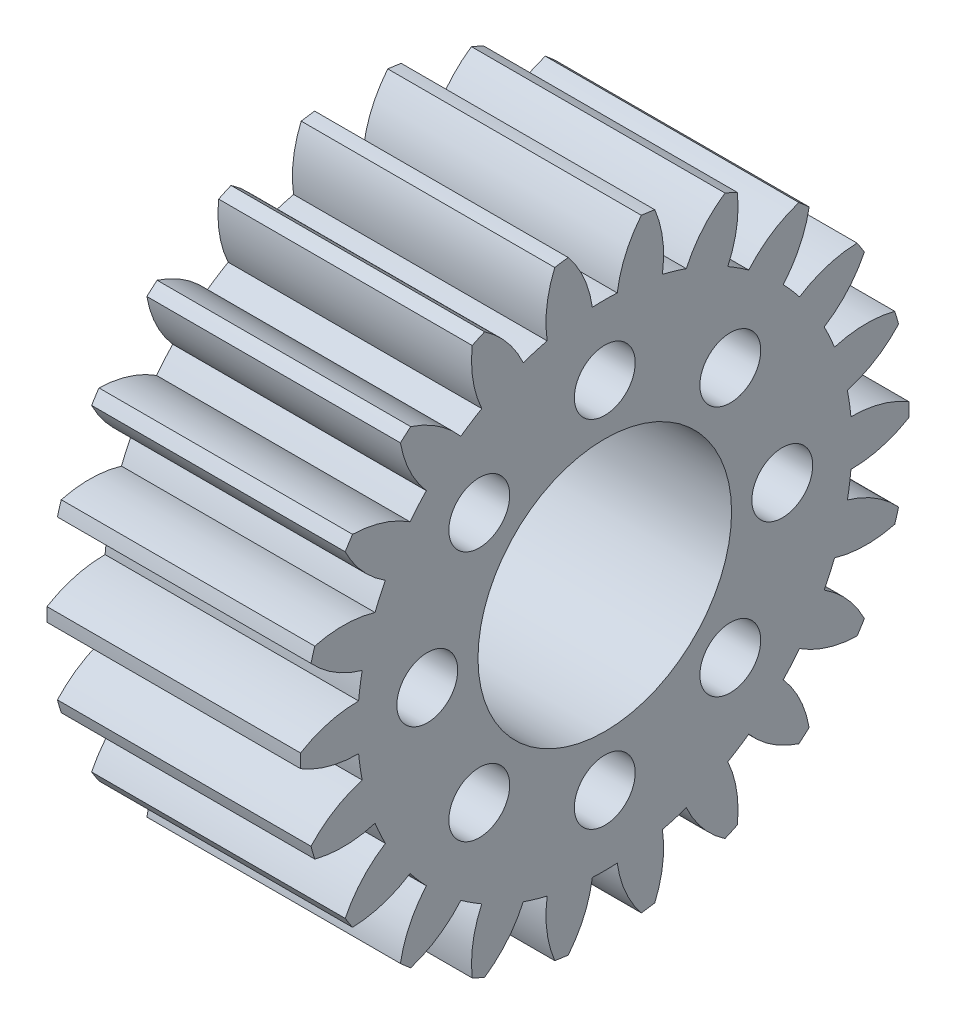
SolidWorks part; units mm, degrees
ref_plane "Plane1" through (0, 0, 0) normal (0, 0, 1) x (1, 0, 0)
ref_plane "Plane2" through (0, 0, 0) normal (0, 1, 0) x (1, 0, 0)
ref_plane "Plane3" through (0, 0, 0) normal (1, 0, 0) x (0, 0, -1)
sketch "HoldingSke" plane through (0, 0, 0) normal (0, 1, 0) x (1, 0, 0)
  line L0 (0, 0) -> (0.9272, -0.3746)
  line L1 (-15, 0) -> (100, 0) construction
  line L2 (0, 0) -> (-2.1039, 2.3779)
  line L3 (0, 0) -> (-11.863, 4.5341)
  line L4 (0, 0) -> (8.0072, 3.2351)
  line L5 (0, 0) -> (-46.8476, -17.4728)
  line L6 (0, 0) -> (-8.2896, -5.593)
  line L7 (-2.1039, 2.3779) -> (8.6586, 51.2059)
  line L8 (-76.2, 54.61) -> (-74.4, 54.61)
  line L9 (-71.009, 38.7566) -> (-53.1078, 45.2721)
  line L10 (-76.2, 71.12) -> (104.1128, 71.12)
  line L11 (0, 0) -> (-10, 0)
  line L12 (-76.2, 101.6) -> (-76.162, 101.6)
  line L13 (24.9733, 27.94) -> (52.9518, 28.4284)
  line L14 (24.9733, 27.94) -> (24.9743, 27.94)
  line L15 (24.9733, 27.94) -> (100.4006, 29.5858)
  line L16 (-63.627, -1) -> (-12.827, -1)
  circle A0 centre (0, 0) radius 5
  circle A1 centre (0, 0) radius 9.749
  circle A2 centre (0, 0) radius 37.5
  circle A3 centre (0, 0) radius 5
  dimension "MHD" = 19.498
  dimension "Hub_dia" = 75
  dimension "Bore" = 10
  dimension "MBD" = 10
  dimension "Num_teeth" = 22
  dimension "Pitch" = 1
  dimension "Overall_len" = 50
  dimension "Show_teeth" = 22
  dimension "Thickness" = 10
  dimension "OAL" = 50.0001
  dimension "T_dim" = 1.8
  dimension "Ap" = 20
  dimension "H" = 19.05
  dimension "Pitch_radius" = 180.3128
  dimension "Width" = 10
  dimension "Backlash" = 0.038
  dimension "Addendum_fac" = 1
  dimension "Dedendum_fac" = 1.25
  dimension "Clearance_fac" = 0.25
  dimension "Dedendum_add" = 0.001
  dimension "Module" = 1
sketch "BasProSke" plane through (0, 0, 0) normal (0, 1, 0) x (1, 0, 0)
  line L0 (-10, 0) -> (60, 0) construction
  line L1 (0, 0) -> (0, 12)
  line L2 (0, 0) -> (10, 0)
  line L3 (10, 0) -> (10, 12)
  line L4 (10, 12) -> (0, 12)
  dimension "Thickness" = 10
  dimension "Diameter" = 24
revolve "Base-Revolve" add sketch "BasProSke" angle 360 about L0
sketch "TooCutSke" plane through (0, 0, 0) normal (1, 0, 0) x (0, 0, -1)
  line L1 (0, 0) -> (0, 107) construction
  line L2 (0, 0) -> (-0.8512, 10.967) construction
  line L3 (0, 0) -> (-3.1242, 21.7296) construction
  line L4 (-0.8512, 10.967) -> (-1.5621, 10.8648) construction
  arc A0 (0.491, 9.7366) -> (-0.491, 9.7366) centre (0, 0) ccw
  arc A1 (1.4609, 11.9363) -> (-1.4609, 11.9363) centre (0, 0) ccw
  circle A2 centre (0, 0) radius 11 construction
  circle A3 centre (0, 0) radius 10.3366 construction
  arc A4 (-0.491, 9.7366) -> (-1.4609, 11.9363) centre (-4.8488, 9.1288) ccw
  arc A5 (1.4609, 11.9363) -> (0.491, 9.7366) centre (4.8488, 9.1288) ccw
  dimension "Root_dia" = 19.498
  dimension "Overcut_dia" = 24.0508
  dimension "Pitch_dia" = 22
  dimension "Base_dia" = 20.6732
  dimension "Flank_rad" = 4.4
  dimension "Half_ang" = 8.182
  dimension "Half_CT" = 0.7182
extrude "ToothCut" cut sketch "TooCutSke" along normal through all
fillet "Breaks" [suppressed] radius 0.02
fillet "RootFillets" [suppressed] radius 0.251
pattern_circular "TeethCuts" count 22 every 16.364 about axis through (-10, 0, 0) along (1, 0, 0) of "ToothCut", "RootFillets", "Breaks"
sketch "HubNeaOneSke" plane through (0, 0, 0) normal (-1, 0, 0) x (0, 0, 1)
  circle A0 centre (0, 0) radius 9.749
  dimension "Diameter" = 19.498
extrude "HubNearOne" [suppressed] add sketch "HubNeaOneSke" along normal blind 40.0001
sketch "HubNeaBotSke" plane through (0, 0, 0) normal (-1, 0, 0) x (0, 0, 1)
  circle A0 centre (0, 0) radius 9.749
  dimension "Diameter" = 19.498
extrude "HubNearBoth" [suppressed] add sketch "HubNeaBotSke" along normal blind 20
ref_plane "FarPln" through (10, 0, 0) normal (1, 0, 0) x (0, 0, -1)
sketch "HubFarSke" plane through (10, 0, 0) normal (1, 0, 0) x (0, 0, -1)
  circle A0 centre (0, 0) radius 9.749
  dimension "Diameter" = 19.498
extrude "HubFar" [suppressed] add sketch "HubFarSke" along normal blind 20
sketch "BorSke" plane through (0, 0, 0) normal (1, 0, 0) x (0, 0, -1)
  circle A0 centre (0, 0) radius 5
  dimension "Diameter" = 10
extrude "Bore" cut sketch "BorSke" along normal mid plane 100.0001
sketch "KeySke" plane through (0, 0, 0) normal (1, 0, 0) x (0, 0, -1)
  line L0 (-2, 0) -> (-2, 6.8)
  line L1 (-2, 6.8) -> (2, 6.8)
  line L2 (2, 6.8) -> (2, 0)
  line L3 (0, 0) -> (0, 34) construction
  line L4 (-2, 0) -> (2, 0)
  dimension "Offset" = 6.8
  dimension "Width" = 4
extrude "Keyway" [suppressed] cut sketch "KeySke" along normal mid plane 100.0001
pattern_circular "Keyway2" [suppressed] count 2 every 90 about axis through (-10, 0, 0) along (1, 0, 0)
hole_wizard "Dégagement M21" positions "Esquisse1" profile "Esquisse2" hole size "M2" standard "ISO" end condition up to next
sketch "Esquisse1" plane through (10, 0, 0) normal (1, 0, 0) x (0, 0, -1)
  point P0 (0, 7)
  point P8 (4.9497, 4.9497)
  point P9 (7, 0)
  point P10 (4.9497, -4.9497)
  point P11 (0, -7)
  point P12 (-4.9497, -4.9497)
  point P13 (-7, 0)
  point P14 (-4.9497, 4.9497)
  point P15 (0, 0)
  dimension "D1" = 8
sketch "Esquisse2" plane through (10, 7, 0) normal (0, 1, 0) x (0, 0, -1)
  line L0 (0, 0) -> (0, 10)
  line L1 (0, 10) -> (1.2, 10)
  line L2 (1.2, 10) -> (1.2, 0)
  line L5 (1.2, 0) -> (0, 0)
  line L11 (0, -6.35) -> (0, 107.95) construction
  dimension "Diamètre du perçage jusqu'au prochain" = 2.4
  dimension "Profondeur du perçage jusqu'au prochain" = 10
equation "' \"Module@HoldingSke\" = 6.35"
equation "' \"Num_teeth@HoldingSke\" = 12"
equation "' \"Ap@HoldingSke\" =  20"
equation "' \"Ap@HoldingSke\" = 20"
equation "' \"Width@HoldingSke\" = 0.5 * 25.4"
equation "' \"Hub_dia@HoldingSke\"= 1 * 25.4"
equation "' \"Hub_dia@HoldingSke\" = 1 * 25.4"
equation "' \"Overall_len@HoldingSke\" = 1.0 * 25.4"
equation "' \"Bore@HoldingSke\" = 0.75 * 25.4"
equation "' \"T_dim@HoldingSke\" = 0.1 * 25.4"
equation "' \"Width@KeySke\" = 0.25 * 25.4"
equation "' \"Show_teeth@HoldingSke\" = 13"
equation "' \"Backlash@HoldingSke\" = 0.009 * 25.4"
equation "' \"Addendum_fac@HoldingSke\" = 1.0"
equation "' \"Dedendum_fac@HoldingSke\" = 1.25"
equation "' \"Dedendum_add@HoldingSke\" = 0.00005 * 25.4"
equation "' \"Clearance_fac@HoldingSke\" = 0.25"
equation "\"Pitch@HoldingSke\" = 1 / \"Module@HoldingSke\""
equation "\"Overcut_dia@TooCutSke\" = (\"Num_teeth@HoldingSke\" + 2 * \"Addendum_fac@HoldingSke\") / \"Pitch@HoldingSke\" + 0.002 * 25.4"
equation "\"Pitch_dia@TooCutSke\" = \"Num_teeth@HoldingSke\" / \"Pitch@HoldingSke\""
equation "\"Base_dia@TooCutSke\" = \"Num_teeth@HoldingSke\" / \"Pitch@HoldingSke\" * cos((\"Ap@HoldingSke\"  * 3.14159265 / 180))"
equation "\"Root_dia@TooCutSke\" = (\"Num_teeth@HoldingSke\" + 2) / \"Pitch@HoldingSke\" - 2 * (\"Addendum_fac@HoldingSke\" + \"Dedendum_fac@HoldingSke\") / \"Pitch@HoldingSke\" - \"Dedendum_add@HoldingSke\" * 2"
equation "\"Half_ang@TooCutSke\" = 180 / \"Num_teeth@HoldingSke\""
equation "\"Half_CT@TooCutSke\" = \"Num_teeth@HoldingSke\" / \"Pitch@HoldingSke\" * sin((3.14159265 / 2 / \"Num_teeth@HoldingSke\")) / 2 - 7 * \"Backlash@HoldingSke\" / 4"
equation "\"Flank_rad@TooCutSke\" = \"Num_teeth@HoldingSke\" / \"Pitch@HoldingSke\" / 5"
equation "\"Radius@RootFillets\" = \"Clearance_fac@HoldingSke\" / \"Pitch@HoldingSke\" + \"Dedendum_add@HoldingSke\""
equation "\"Break_rad@Breaks\" = 0.02 / \"Pitch@HoldingSke\""
equation "\"Thickness@HoldingSke\" = \"Width@HoldingSke\""
equation "\"OAL@HoldingSke\" = \"Thickness@HoldingSke\""
equation "\"MHD@HoldingSke\" = (\"Num_teeth@HoldingSke\" + 2) / \"Pitch@HoldingSke\" - 2 * (\"Addendum_fac@HoldingSke\" + \"Dedendum_fac@HoldingSke\")  / \"Pitch@HoldingSke\" - \"Dedendum_add@HoldingSke\" * 2"
equation "\"MBD@HoldingSke\" = (\"Num_teeth@HoldingSke\" + 2) / \"Pitch@HoldingSke\" - 2 * (\"Addendum_fac@HoldingSke\" + \"Dedendum_fac@HoldingSke\")  / \"Pitch@HoldingSke\" - \"Dedendum_add@HoldingSke\" * 2 - 0.002 * 25.4"
equation "\"MHD@HoldingSke\" = ((sgn( \"MHD@HoldingSke\" - \"Hub_dia@HoldingSke\" )-1)*( \"MHD@HoldingSke\" - \"Hub_dia@HoldingSke\" ))/-2+ \"Hub_dia@HoldingSke\""
equation "\"MBD@HoldingSke\" = ((sgn( \"MBD@HoldingSke\" - \"Bore@HoldingSke\" )-1)*( \"MBD@HoldingSke\" - \"Bore@HoldingSke\" ))/-2+ \"Bore@HoldingSke\""
equation "\"OAL@HoldingSke\" = ((sgn( \"OAL@HoldingSke\" - \"Overall_len@HoldingSke\" )+1)*( \"OAL@HoldingSke\" - \"Overall_len@HoldingSke\" ))/2 + \"Overall_len@HoldingSke\" + 0.000002 * 25.4"
equation "\"Num_teeth@TeethCuts\" = int( \"Show_teeth@HoldingSke\" ) + 1"
equation "\"Num_teeth@TeethCuts\" = ((sgn( \"Num_teeth@TeethCuts\" - \"Num_teeth@HoldingSke\" )-1)*( \"Num_teeth@TeethCuts\" - \"Num_teeth@HoldingSke\" ))/-2+ \"Num_teeth@HoldingSke\""
equation "\"Num_teeth@TeethCuts\" = ((sgn( \"Num_teeth@TeethCuts\" - 2.0)+1)*( \"Num_teeth@TeethCuts\" - 2.0))/2 +2.0"
equation "\"Angle@TeethCuts\" = 360.0 / \"Num_teeth@HoldingSke\""
equation "\"Diameter@BasProSke\" = (\"Num_teeth@HoldingSke\" + 2 * \"Addendum_fac@HoldingSke\") / \"Pitch@HoldingSke\""
equation "\"Thickness@BasProSke\"  = \"Thickness@HoldingSke\""
equation "' \"Fillet_rad@BasProSke\" =  \"Thickness@HoldingSke\" * 0.05"
equation "' \"Fillet_rad@BasProSke\" = \"Thickness@HoldingSke\" * 0.05"
equation "\"MHD@HoldingSke\" = ((sgn( \"MHD@HoldingSke\" - \"Root_dia@TooCutSke\" )-1)*( \"MHD@HoldingSke\" - \"Root_dia@TooCutSke\" ))/-2+ \"Root_dia@TooCutSke\""
equation "\"Diameter@HubNeaOneSke\" = \"MHD@HoldingSke\""
equation "\"Length@HubNearOne\" = \"OAL@HoldingSke\" - \"Thickness@BasProSke\""
equation "\"Diameter@HubNeaBotSke\" = \"MHD@HoldingSke\""
equation "\"Length@HubNearBoth\" = ( \"OAL@HoldingSke\" - \"Thickness@BasProSke\" ) / 2.0"
equation "\"Thickness@FarPln\" = \"Thickness@BasProSke\""
equation "\"Diameter@HubFarSke\" = \"MHD@HoldingSke\""
equation "\"Length@HubFar\" = ( \"OAL@HoldingSke\" - \"Thickness@BasProSke\" ) / 2.0"
equation "\"Diameter@BorSke\" = \"MBD@HoldingSke\""
equation "\"D1@Bore\" = \"OAL@HoldingSke\" * 2.0"
equation "\"D1@Keyway\" = \"OAL@HoldingSke\" * 2.0"
equation "\"Offset@KeySke\" = \"T_dim@HoldingSke\" + \"MBD@HoldingSke\" / 2.0"
